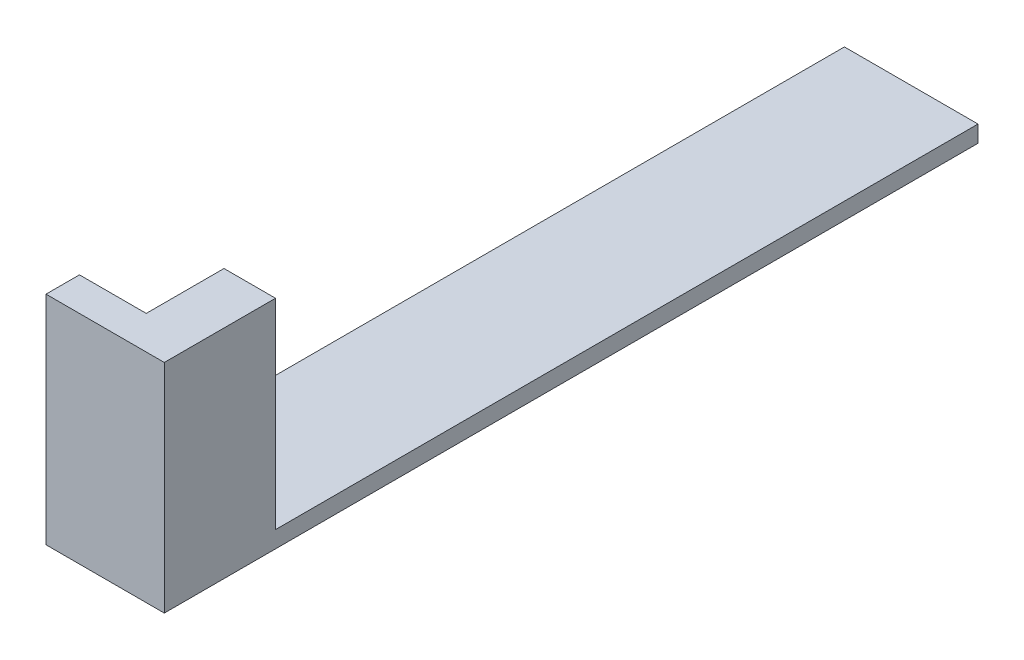
SolidWorks part; units mm, degrees
ref_plane "Piano frontale" through (0, 0, 0) normal (0, 0, 1) x (1, 0, 0)
ref_plane "Piano superiore" through (0, 0, 0) normal (0, 1, 0) x (1, 0, 0)
ref_plane "Piano destro" through (0, 0, 0) normal (1, 0, 0) x (0, 0, -1)
sketch "Schizzo1" plane through (0, 0, 0) normal (0, 1, 0) x (1, 0, 0)
  line L1 (0, 0) -> (8, 0)
  line L2 (0, 0) -> (0, 42.07)
  line L3 (0, 42.07) -> (8, 42.07)
  line L4 (8, 0) -> (8, 42.07)
  dimension "D1" = 8
  dimension "D2" = 42.07
extrude "Estrusione-Estrusione1" add sketch "Schizzo1" along normal blind 1
sketch "Schizzo2" plane through (0, 0, 0) normal (0, 0, 1) x (1, 0, 0)
  line L0 (0, 0) -> (8, 0) construction
  line L1 (4.9152, 0) -> (8, 0)
  line L2 (4.9152, 0) -> (4.9152, 1)
  line L3 (4.9152, 1) -> (8, 1)
  line L4 (8, 0) -> (8, 1)
extrude "Estrusione-Estrusione2" add sketch "Schizzo2" along normal blind 4.66
sketch "Schizzo3" plane through (0, 0, 4.66) normal (0, 0, 1) x (1, 0, 0)
  line L0 (4.9152, 1) -> (4.9152, 0) construction
  line L1 (4.9152, 1) -> (8, 1)
  line L2 (4.9152, 1) -> (4.9152, 0)
  line L3 (4.9152, 0) -> (8, 0)
  line L4 (8, 1) -> (8, 0)
  line L5 (8, 1) -> (4.9152, 1) construction
extrude "Estrusione-Estrusione3" add sketch "Schizzo3" along normal blind 2
sketch "Schizzo4" plane through (4.9152, 0, 0) normal (-1, 0, 0) x (0, 0, 1)
  line L0 (6.66, 0) -> (0, 0) construction
  line L1 (4.6569, 0) -> (6.66, 0)
  line L2 (4.6569, 0) -> (4.6569, 1)
  line L3 (4.6569, 1) -> (6.66, 1)
  line L4 (6.66, 0) -> (6.66, 1)
  line L5 (6.66, 1) -> (6.66, 0) construction
  line L6 (6.66, 1) -> (0, 1) construction
extrude "Estrusione-Estrusione4" add sketch "Schizzo4" along normal blind 4
sketch "Schizzo5" plane through (0, 1, 0) normal (0, 1, 0) x (1, 0, 0)
  line L1 (8, -6.66) -> (0.9152, -6.66)
  line L2 (8, -6.66) -> (8, -4.6569)
  line L3 (8, -4.6569) -> (0.9152, -4.6569)
  line L4 (0.9152, -6.66) -> (0.9152, -4.6569)
extrude "Estrusione-Estrusione5" add sketch "Schizzo5" along normal blind 12
sketch "Schizzo7" plane through (0, 1, 0) normal (0, 1, 0) x (1, 0, 0)
  line L1 (4.9152, 0) -> (8, 0)
  line L2 (4.9152, 0) -> (4.9152, -4.6569)
  line L3 (4.9152, -4.6569) -> (8, -4.6569)
  line L4 (8, 0) -> (8, -4.6569)
extrude "Estrusione-Estrusione7" add sketch "Schizzo7" along normal blind 12
